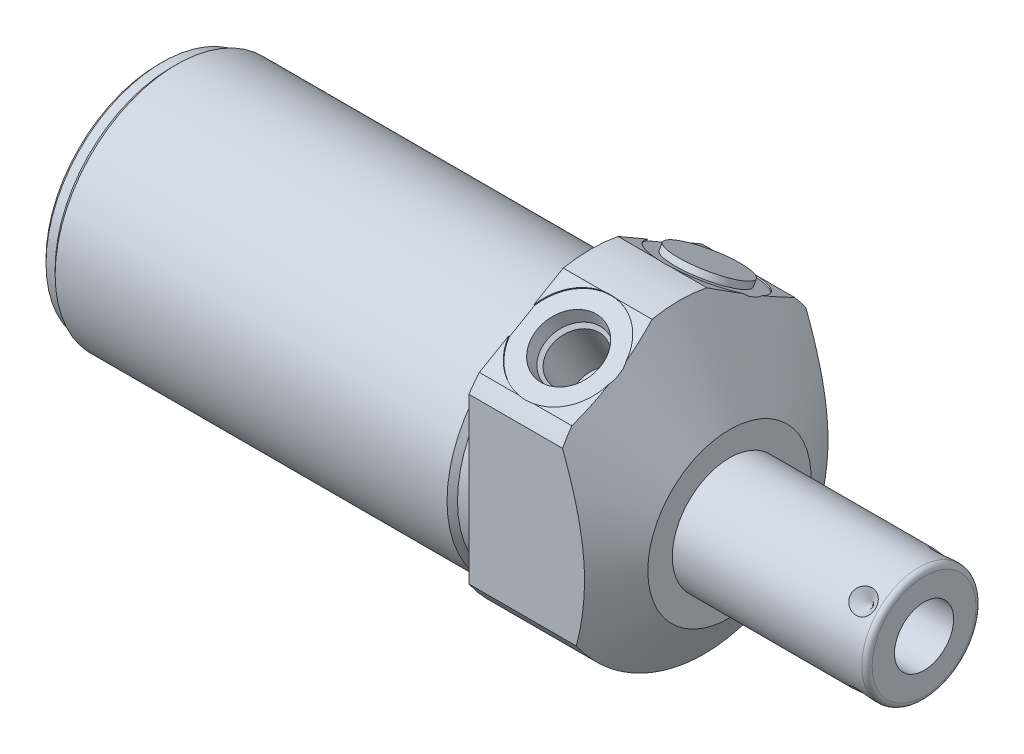
SolidWorks part; units mm, degrees
material "Alloy Steel"
ref_plane "Front Plane" through (0, 0, 0) normal (0, 0, 1) x (1, 0, 0)
ref_plane "Top Plane" through (0, 0, 0) normal (0, 1, 0) x (1, 0, 0)
ref_plane "Right Plane" through (0, 0, 0) normal (1, 0, 0) x (0, 0, -1)
ref_plane "Plane1" through (0, 0, 0) normal (1, 0, 0) x (0, 0, -1)
sketch "Sketch1" plane through (0, 0, 0) normal (1, 0, 0) x (0, 0, -1)
  circle A0 centre (0, 0) radius 28.575
  dimension "D1" = 57.15
extrude "Extrude1" add sketch "Sketch1" along normal blind 27.0002 and the other way blind 84.1248
ref_plane "Plane2" through (0, 0, 0) normal (1, 0, 0) x (0, 0, -1)
sketch "Sketch2" plane through (0, 0, 0) normal (1, 0, 0) x (0, 0, -1)
  line L0 (-25.9842, -4.191) -> (25.9842, -4.191) construction
  circle A0 centre (0, -4.191) radius 23.622
  circle A2 centre (0, 0) radius 28.575
  circle A3 centre (0, 0) radius 28.575
  dimension "D2" = 47.244
  dimension "D1" = 4.191
  dimension "D3" = 0
extrude "Cut-Extrude1" cut sketch "Sketch2" against normal up to next
ref_plane "Plane4" through (0, 0, 0) normal (-1, 0, 0) x (0, 0, 1)
sketch "Sketch4" plane through (0, 0, 0) normal (-1, 0, 0) x (0, 0, 1)
  line L0 (23.6855, -25.6662) -> (23.6855, 17.4761)
  line L1 (23.6855, 17.4761) -> (0, 31.1509)
  line L2 (-23.6855, -25.6662) -> (-23.6855, 17.4761)
  line L3 (-23.6855, 17.4761) -> (0, 31.1509)
  line L4 (0, -31.5613) -> (0, 34.1372) construction
  arc A2 (23.6855, -25.6662) -> (-23.6855, -25.6662) centre (0, 0) ccw
  dimension "D4" = 69.85
  dimension "D1" = 47.371
  dimension "D2" = 30.607
  dimension "D3" = 120
extrude "Cut-Extrude3" cut sketch "Sketch4" against normal up to next
ref_plane "Plane6" through (0, 0, 0) normal (0, 0, 1) x (1, 0, 0)
sketch "Sketch6" plane through (0, 0, 0) normal (0, 0, 1) x (1, 0, 0)
  line L0 (0.7504, 57.15) -> (27.0002, 11.684)
  line L1 (-0.5621, -4.191) -> (28.3127, -4.191) construction
  line L2 (-84.1248, -4.191) -> (0, -4.191) construction
  line L3 (27.0002, 11.684) -> (27.0002, 57.15)
  line L4 (27.0002, 57.15) -> (0.7504, 57.15)
  line L5 (27.0002, 15.9852) -> (27.0002, -15.9852) construction
  dimension "D1" = 60
  dimension "D2" = 31.75
  dimension "D3" = 122.682
revolve "Cut-Revolve2" cut sketch "Sketch6" angle 360 about L1
ref_plane "Plane7" through (9.0932, 23.1369, 13.3727) normal (1, 0, 0) x (0, 0.5, -0.866)
sketch "S2D0002" plane through (9.0932, 23.1369, 13.3727) normal (1, 0, 0) x (0, 0.5, -0.866)
  line L0 (0, 0) -> (6.1849, 0)
  line L1 (6.1849, 0) -> (5.6423, -2.5527)
  line L2 (5.6423, -2.5527) -> (4.9784, -3.2166)
  line L3 (4.9784, -3.2166) -> (4.9784, -13.462)
  line L4 (4.9784, -13.462) -> (0, -13.462)
  line L5 (0, -13.462) -> (0, 0)
  line L6 (0, -14.1351) -> (0, 0.6731) construction
  dimension "D1" = 13.462
revolve "Cut-Revolve3" cut sketch "S2D0002" angle 360 about L6
ref_plane "Plane8" through (9.0932, 23.1369, -13.3727) normal (1, 0, 0) x (0, -0.5, -0.866)
sketch "Sketch8" plane through (9.0932, 23.1369, -13.3727) normal (1, 0, 0) x (0, -0.5, -0.866)
  line L0 (0, 0) -> (6.1849, 0)
  line L1 (6.1849, 0) -> (5.6423, -2.5527)
  line L2 (5.6423, -2.5527) -> (4.9784, -3.2166)
  line L3 (4.9784, -3.2166) -> (4.9784, -13.462)
  line L4 (4.9784, -13.462) -> (0, -13.462)
  line L5 (0, -13.462) -> (0, 0)
  line L6 (0, -14.1351) -> (0, 0.6731) construction
  dimension "D1" = 13.462
revolve "Cut-Revolve4" cut sketch "Sketch8" angle 360 about L6
ref_plane "Plane10" through (0, 0, 0) normal (0, 0, 1) x (1, 0, 0)
sketch "Sketch18" plane through (0, 23.3632, 13.4887) normal (0, 0.866, 0.5) x (1, 0, 0)
  circle A0 centre (9.0932, -0.0127) radius 9.525
  dimension "D1" = 19.05
extrude "Cut-Extrude4" cut sketch "Sketch18" against normal blind 0.254
sketch "Sketch19" plane through (0, 23.3632, -13.4887) normal (0, 0.866, -0.5) x (1, 0, 0)
  circle A0 centre (9.0932, 0.0127) radius 9.525
  circle A1 centre (9.0932, 0.0127) radius 6.1849 construction
  dimension "D1" = 19.05
extrude "Cut-Extrude5" cut sketch "Sketch19" against normal blind 0.254
sketch "Sketch10" plane through (0, 0, 0) normal (0, 0, 1) x (1, 0, 0)
  line L0 (0, 19.431) -> (0, 18.415)
  line L1 (0, 18.415) -> (-3.302, 18.415)
  line L2 (-3.302, 18.415) -> (-4.318, 19.431)
  line L3 (-4.5339, -4.191) -> (0.2159, -4.191) construction
  line L4 (0, 19.431) -> (-4.318, 19.431)
  line L5 (-84.1248, -4.191) -> (0, -4.191) construction
  line L6 (0, 19.431) -> (-84.1248, 19.431) construction
  line L7 (0, 21.9392) -> (0, 18.6529) construction
  dimension "D1" = 45.212
  dimension "D2" = 45
  dimension "D3" = 3.302
revolve "Cut-Revolve6" cut sketch "Sketch10" angle 360 about L3
ref_plane "Plane12" through (0, 0, 0) normal (0, 0, 1) x (1, 0, 0)
sketch "Sketch12" plane through (0, 0, 0) normal (0, 0, 1) x (1, 0, 0)
  line L0 (-84.1248, 19.431) -> (-84.1248, 18.415)
  line L1 (-84.1248, 18.415) -> (-81.5848, 18.415)
  line L2 (-81.5848, 18.415) -> (-80.5688, 19.431)
  line L3 (-84.3026, -4.191) -> (-80.391, -4.191) construction
  line L4 (-84.1248, 19.431) -> (-80.5688, 19.431)
  line L5 (-84.1248, -4.191) -> (-4.318, -4.191) construction
  line L6 (-4.318, 19.431) -> (-84.1248, 19.431) construction
  line L7 (-84.1248, 19.431) -> (-84.1248, -27.813) construction
  dimension "D1" = 45.212
  dimension "D2" = 45
  dimension "D3" = 2.54
revolve "Cut-Revolve8" cut sketch "Sketch12" angle 360 about L3
chamfer "Chamfer1" distance 0.762 angle 45 1 edges at (-84.1248, -4.191, 22.606)
ref_plane "Plane13" through (0, 0, 0) normal (0, 0, 1) x (0, -1, 0)
sketch "Sketch13" plane through (0, 0, 0) normal (0, 0, 1) x (0, -1, 0)
  line L0 (4.191, 27.0002) -> (4.191, 64.8716)
  line L1 (4.191, 64.8716) -> (14.2875, 64.8716)
  line L2 (15.3035, 63.8556) -> (15.3035, 27.0002)
  line L3 (15.3035, 27.0002) -> (4.191, 27.0002)
  line L4 (4.191, 25.1066) -> (4.191, 66.7652) construction
  line L5 (4.191, -80.5688) -> (4.191, -4.318) construction
  line L6 (20.066, 27.0002) -> (-11.684, 27.0002) construction
  line L7 (-18.415, 0) -> (26.797, 0) construction
  arc A0 (15.3035, 63.8556) -> (14.2875, 64.8716) centre (14.2875, 63.8556) ccw
  dimension "D3" = 1.016
  dimension "D1" = 22.225
  dimension "D2" = 64.8716
revolve "Revolve1" add sketch "Sketch13" angle 360 about L4
ref_plane "Plane14" through (64.8716, -9.9441, 0) normal (0, 0, 1) x (0, -1, 0)
sketch "S2D0001" plane through (64.8716, -9.9441, 0) normal (0, 0, 1) x (0, -1, 0)
  line L0 (0, 0) -> (0, -17.018)
  line L1 (0, -17.018) -> (-5.7531, -20.4748)
  line L2 (0, 0) -> (-5.7531, 0)
  line L3 (-5.7531, 0) -> (-5.7531, -20.4748)
  line L4 (-5.7531, -21.4986) -> (-5.7531, 1.0237) construction
  line L5 (-5.7531, -1.016) -> (-5.7531, -37.8714) construction
  line L6 (4.3434, 0) -> (-15.8496, 0) construction
  dimension "D1" = 11.5062
  dimension "D2" = 59
  dimension "D3" = 17.018
revolve "Cut-Revolve9" cut sketch "S2D0001" angle 360 about L4
ref_plane "Plane15" through (27.0002, 23.1432, -13.3617) normal (0, -0.866, 0.5) x (0, -0.5, -0.866)
sketch "Sketch15" plane through (27.0002, 23.1432, -13.3617) normal (0, -0.866, 0.5) x (0, -0.5, -0.866)
  circle A0 centre (0.0127, -17.907) radius 6.9469
  arc A1 (-2.4139, -8.6963) -> (-9.4205, -16.5878) centre (0.0127, -17.907) ccw construction
  dimension "D1" = 13.8938
extrude "Extrude2" add sketch "Sketch15" against normal blind 1.27
ref_plane "Plane16" through (60.9092, -15.3035, 0) normal (0, 0, 1) x (-1, 0, 0)
ref_plane "Plane17" through (0, -2.0955, -2.0955) normal (0, 0.7071, 0.7071) x (-1, 0, 0)
sketch "Sketch16" plane through (60.9092, 3.6667, -7.8577) normal (0, -0.7071, -0.7071) x (-1, 0, 0)
  line L0 (0, 0) -> (2.413, 0)
  line L1 (2.413, 0) -> (0, -2.413)
  line L2 (0, 0) -> (0, -2.413)
  line L3 (0, -4.4865) -> (0, 0.1207) construction
  line L4 (-3.9624, -1.016) -> (-3.9624, -21.209) construction
  line L5 (33.909, 0) -> (-2.9464, 0) construction
  dimension "D1" = 45
  dimension "D2" = 3.9624
  dimension "D3" = 4.826
revolve "Cut-Revolve10" cut sketch "Sketch16" angle 360 about L3
pattern_circular "CirPattern1" count 4 over 360 about axis through (25.1066, -4.191, 0) along (-1, 0, 0) of "Cut-Revolve10"
